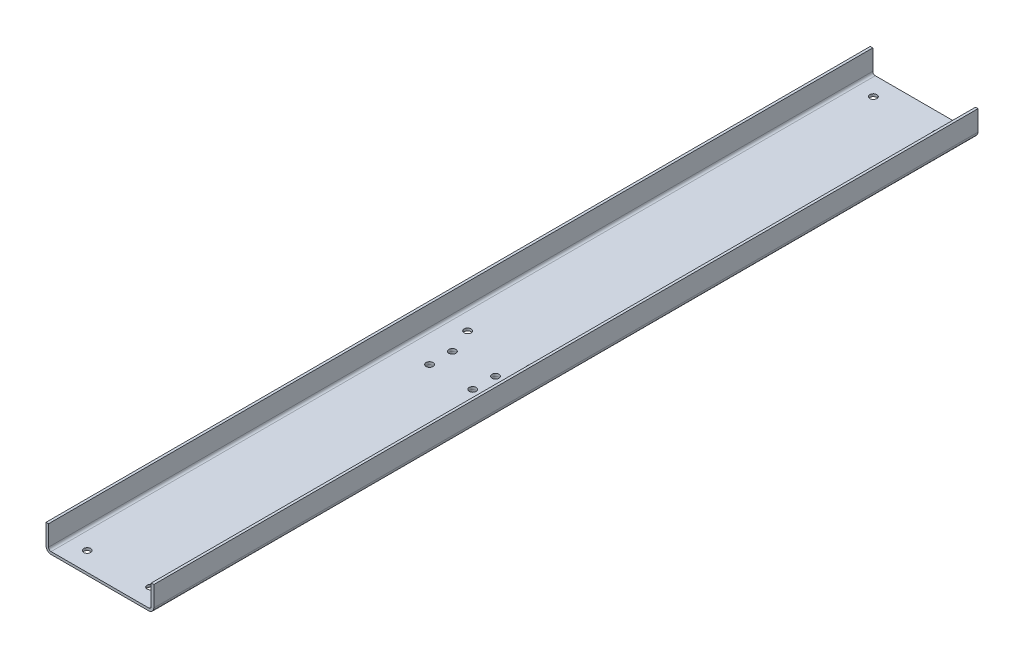
SolidWorks part; units mm, degrees
ref_plane "Front" through (0, 0, 0) normal (0, 0, 1) x (1, 0, 0)
ref_plane "Top" through (0, 0, 0) normal (0, 1, 0) x (1, 0, 0)
ref_plane "Right" through (0, 0, 0) normal (1, 0, 0) x (0, 0, -1)
sketch "Sketch1" plane through (0, 0, 0) normal (0, 0, 1) x (1, 0, 0)
  line L0 (0, 32.15) -> (0, -9.5658) construction
  line L1 (40.5, 20) -> (42.5, 20)
  line L2 (-42.5, 0) -> (42.5, 0)
  line L3 (-42.5, 0) -> (-42.5, 20)
  line L4 (-42.5, 20) -> (-40.5, 20)
  line L5 (42.5, 0) -> (42.5, 20)
  line L6 (-40.5, 2) -> (40.5, 2)
  line L7 (-40.5, 2) -> (-40.5, 20)
  line L9 (40.5, 2) -> (40.5, 20)
  dimension "D1" = 85
  dimension "D2" = 2
  dimension "D3" = 2
  dimension "D4" = 20
extrude "Boss-Extrude1" add sketch "Sketch1" along normal blind 650
fillet "Fillet1" radius 2 2 edges at (40.5, 2, 325) (-40.5, 2, 325)
fillet "Fillet2" radius 4 2 edges at (42.5, 0, 325) (-42.5, 0, 325)
sketch "Sketch2" plane through (0, 0, 0) normal (0, -1, 0) x (1, 0, 0)
  line L0 (0, 0) -> (0, 679.9436) construction
  line L1 (23, 379) -> (-23, 379)
  line L2 (23, 379) -> (23, 349)
  line L3 (23, 349) -> (-23, 349)
  line L4 (-23, 379) -> (-23, 349)
  line L5 (51.8366, 364) -> (-65.1678, 364) construction
  dimension "D1" = 46
  dimension "D2" = 30
  dimension "D3" = 364
extrude "Boss-Extrude2" add sketch "Sketch2" along normal blind 6 separate body
chamfer "Chamfer1" distance 3 angle 45 4 edges at (-23, -3, 349) (-23, -3, 379) (23, -3, 349) (23, -3, 379)
hole_wizard "M5 Clearance Hole1" positions "Sketch4" profile "Sketch3" hole size "M5" standard "JIS" end condition through all
sketch "Sketch4" plane through (0, 2, 0) normal (0, 1, 0) x (-1, 0, 0)
  line L0 (-38.5, 0) -> (38.5, 0) construction
  line L2 (0, -21.5027) -> (0, 672.4051) construction
  point P0 (25, 15)
  point P1 (25, 635)
  point P9 (-25, 15)
  point P11 (-25, 335)
  point P13 (25, 335)
  point P15 (-25, 635)
  dimension "D1" = 15
  dimension "D2" = 50
  dimension "D3" = 620
  dimension "D4" = 335
sketch "Sketch3" plane through (-25, 2, 15) normal (1, 0, 0) x (0, 0, 1)
  line L0 (0, 0) -> (0, 8)
  line L1 (0, 8) -> (2.75, 8)
  line L2 (2.75, 8) -> (2.75, 0)
  line L5 (2.75, 0) -> (0, 0)
  line L11 (0, -6.35) -> (0, 107.95) construction
  dimension "通し穴の直径" = 5.5
  dimension "通し穴の深さ" = 8
hole_wizard "M5 Clearance Hole2" positions "Sketch6" profile "Sketch5" hole size "M5" standard "JIS" end condition through all
sketch "Sketch6" plane through (0, 2, 0) normal (0, 1, 0) x (-1, 0, 0)
  line L0 (0, -26.2206) -> (0, 390.4042) construction
  line L3 (-50.7021, 364) -> (53.6731, 364) construction
  point P0 (-17, 355)
  point P1 (17, 355)
  point P3 (17, 373)
  point P5 (-17, 373)
  dimension "D2" = 34
  dimension "D3" = 18
  dimension "D4" = 364
sketch "Sketch5" plane through (17, 2, 355) normal (1, 0, 0) x (0, 0, 1)
  line L0 (0, 0) -> (0, 8)
  line L1 (0, 8) -> (2.75, 8)
  line L2 (2.75, 8) -> (2.75, 0)
  line L5 (2.75, 0) -> (0, 0)
  line L11 (0, -6.35) -> (0, 107.95) construction
  dimension "通し穴の直径" = 5.5
  dimension "通し穴の深さ" = 8
